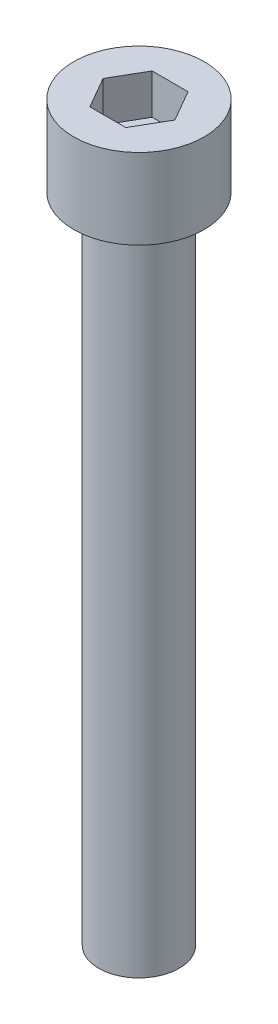
SolidWorks part; units mm, degrees
material "AISI 304"
ref_plane "前视基准面" through (0, 0, 0) normal (0, 0, 1) x (1, 0, 0)
ref_plane "上视基准面" through (0, 0, 0) normal (0, 1, 0) x (1, 0, 0)
ref_plane "右视基准面" through (0, 0, 0) normal (1, 0, 0) x (0, 0, -1)
sketch "草图1" plane through (0, 0, 0) normal (0, 1, 0) x (1, 0, 0)
  circle A0 centre (0, 0) radius 6.5
  dimension "D1" = 13
extrude "杯头" add sketch "草图1" along normal blind 8
sketch "草图2" plane through (0, 8, 0) normal (0, 1, 0) x (1, 0, 0)
  line L1 (3.5796, 0) -> (1.7898, 3.1)
  line L2 (1.7898, 3.1) -> (-1.7898, 3.1)
  line L3 (-1.7898, 3.1) -> (-3.5796, 0)
  line L4 (-3.5796, 0) -> (-1.7898, -3.1)
  line L5 (-1.7898, -3.1) -> (1.7898, -3.1)
  line L6 (1.7898, -3.1) -> (3.5796, 0)
  circle A0 centre (0, 0) radius 3.1 construction
  dimension "D1" = 6.2
extrude "内六角口" cut sketch "草图2" against normal blind 4
sketch "草图3" plane through (0, 0, 0) normal (0, -1, 0) x (1, 0, 0)
  circle A0 centre (0, 0) radius 4
  dimension "D1" = 8
extrude "螺纹长" add sketch "草图3" along normal blind 65
